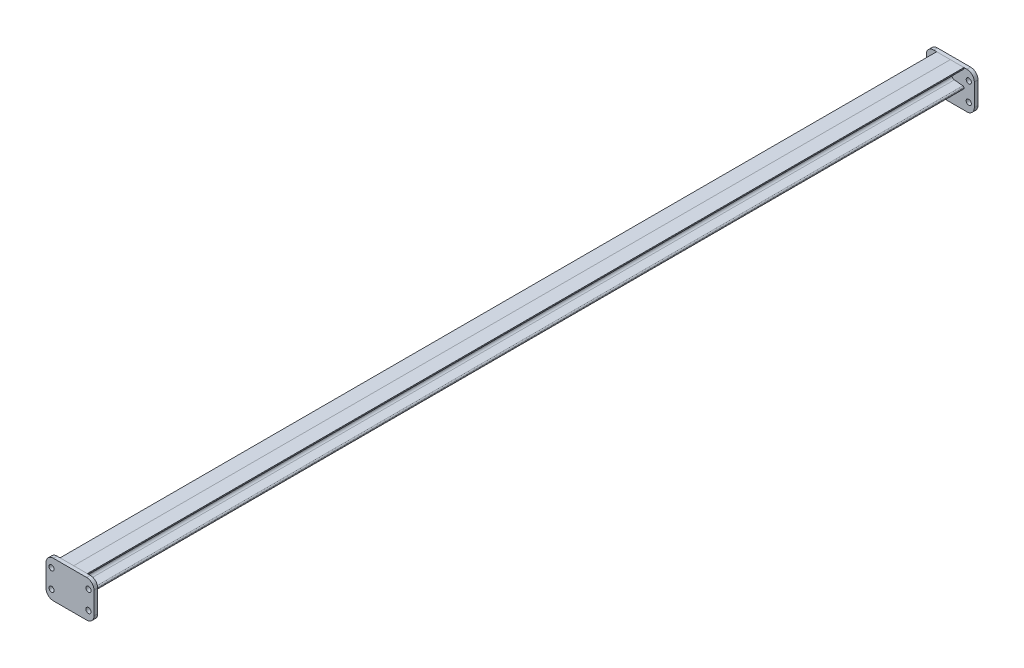
SolidWorks part; units mm, degrees
material "普通碳钢"
ref_plane "前视基准面" through (0, 0, 0) normal (0, 0, 1) x (1, 0, 0)
ref_plane "上视基准面" through (0, 0, 0) normal (0, 1, 0) x (1, 0, 0)
ref_plane "右视基准面" through (0, 0, 0) normal (1, 0, 0) x (0, 0, -1)
sketch "草图1" plane through (0, 0, 0) normal (1, 0, 0) x (0, 0, -1)
  line L0 (0, 0) -> (2374, 0)
  dimension "D1" = 2374
other "槽钢 5#(1)"
ref_plane "基准面1" through (0, 0, 0) normal (0, 0, -1) x (1, 0, 0)
sketch "草图12" plane through (0, 0, 0) normal (0, 0, -1) x (1, 0, 0)
  line L0 (0, -25) -> (37, -25)
  line L1 (37, -25) -> (37, -22.7923)
  line L2 (33.8482, -19.3097) -> (10.8035, -17.0055)
  line L3 (4.5, -10.0402) -> (4.5, 10.0402)
  line L4 (10.8035, 17.0055) -> (33.8482, 19.3097)
  line L5 (37, 22.7923) -> (37, 25)
  line L6 (37, 25) -> (0, 25)
  line L7 (0, 25) -> (0, -25)
  line L8 (20.75, 18) -> (20.75, -18) construction
  line L9 (0, 0) -> (4.5, 0) construction
  line L10 (4.5, 10.0402) -> (4.5, 35) construction
  line L11 (4.5, 35) -> (20.75, 35) construction
  line L12 (20.75, 35) -> (37, 35) construction
  line L13 (37, 35) -> (37, 25) construction
  line L14 (20.75, 35) -> (20.75, 18) construction
  arc A0 (10.8035, -17.0055) -> (4.5, -10.0402) centre (11.5, -10.0402) cw
  arc A1 (4.5, 10.0402) -> (10.8035, 17.0055) centre (11.5, 10.0402) cw
  arc A2 (37, -22.7923) -> (33.8482, -19.3097) centre (33.5, -22.7923) ccw
  arc A3 (33.8482, 19.3097) -> (37, 22.7923) centre (33.5, 22.7923) ccw
  point P2 (0, 0)
  point P19 (0, -25)
  point P20 (0, 25)
  point P22 (0, -25)
  point P23 (37, -25)
  point P24 (37, 25)
  point P26 (37, -19.6248)
  point P27 (11.5, 10.0402)
  point P28 (11.5, -10.0402)
  point P29 (37, 19.6248)
  dimension "D7" = 7
  dimension "D9" = 3.5
  dimension "D1" = 5.71
  dimension "D2" = 10
  dimension "D3" = 50
  dimension "D4" = 37
  dimension "D5" = 4.5
  dimension "D6" = 7
  dimension "D8" = 5.71
other "槽钢 5#(2)"
ref_plane "基准面2" through (0, 0, 0) normal (0, 0, -1) x (-1, 0, 0)
sketch "草图13" plane through (0, 0, 0) normal (0, 0, -1) x (-1, 0, 0)
  line L0 (0, -25) -> (37, -25)
  line L1 (37, -25) -> (37, -22.7923)
  line L2 (33.8482, -19.3097) -> (10.8035, -17.0055)
  line L3 (4.5, -10.0402) -> (4.5, 10.0402)
  line L4 (10.8035, 17.0055) -> (33.8482, 19.3097)
  line L5 (37, 22.7923) -> (37, 25)
  line L6 (37, 25) -> (0, 25)
  line L7 (0, 25) -> (0, -25)
  line L8 (20.75, 18) -> (20.75, -18) construction
  line L9 (0, 0) -> (4.5, 0) construction
  line L10 (4.5, 10.0402) -> (4.5, 35) construction
  line L11 (4.5, 35) -> (20.75, 35) construction
  line L12 (20.75, 35) -> (37, 35) construction
  line L13 (37, 35) -> (37, 25) construction
  line L14 (20.75, 35) -> (20.75, 18) construction
  arc A0 (10.8035, -17.0055) -> (4.5, -10.0402) centre (11.5, -10.0402) cw
  arc A1 (4.5, 10.0402) -> (10.8035, 17.0055) centre (11.5, 10.0402) cw
  arc A2 (37, -22.7923) -> (33.8482, -19.3097) centre (33.5, -22.7923) ccw
  arc A3 (33.8482, 19.3097) -> (37, 22.7923) centre (33.5, 22.7923) ccw
  point P2 (0, 0)
  point P19 (0, -25)
  point P20 (0, 25)
  point P22 (0, -25)
  point P23 (37, -25)
  point P24 (37, 25)
  point P26 (37, -19.6248)
  point P27 (11.5, 10.0402)
  point P28 (11.5, -10.0402)
  point P29 (37, 19.6248)
  dimension "D7" = 7
  dimension "D9" = 3.5
  dimension "D1" = 5.71
  dimension "D2" = 10
  dimension "D3" = 50
  dimension "D4" = 37
  dimension "D5" = 4.5
  dimension "D6" = 7
  dimension "D8" = 5.71
sketch "草图14" plane through (0, 0, 0) normal (0, 0, 1) x (1, 0, 0)
  line L0 (0, 25) -> (37, 25) construction
  line L1 (75, 0) -> (-65, 0) construction
  line L2 (45, 25) -> (-45, 25)
  line L3 (65, 5) -> (65, -55)
  line L4 (45, -75) -> (-45, -75)
  line L5 (-65, 5) -> (-65, -55)
  line L6 (75, -50) -> (-65, -50) construction
  line L7 (75, 25) -> (-65, 25) construction
  arc A0 (-45, -75) -> (-65, -55) centre (-45, -55) cw
  arc A1 (65, -55) -> (45, -75) centre (45, -55) cw
  arc A2 (45, 25) -> (65, 5) centre (45, 5) cw
  arc A3 (-45, 25) -> (-65, 5) centre (-45, 5) ccw
  point P13 (-65, -75)
  point P19 (65, 25)
  dimension "D5" = 20
  dimension "D1" = 130
  dimension "D2" = 100
  dimension "D3" = 25
  dimension "D4" = 50
extrude "凸台-拉伸1" add sketch "草图14" along normal blind 10 separate body
sketch "草图15" plane through (0, 0, 10) normal (0, 0, 1) x (1, 0, 0)
  line L0 (0, 25) -> (0, -75) construction
  line L1 (45, 25) -> (-45, 25) construction
  line L2 (-45, -75) -> (45, -75) construction
  line L5 (-50, 25) -> (-50, -75) construction
  line L7 (50, 25) -> (50, -75) construction
  line L8 (-65, 0) -> (65, 0) construction
  line L9 (-65, 5) -> (-65, -55) construction
  line L10 (65, -55) -> (65, 5) construction
  line L11 (-65, -50) -> (65, -50) construction
  circle A0 centre (-50, 0) radius 7
  circle A1 centre (-50, -50) radius 7
  circle A2 centre (50, 0) radius 7
  circle A3 centre (50, -50) radius 7
  dimension "D5" = 14
  dimension "D1" = 50
  dimension "D2" = 50
  dimension "D3" = 50
  dimension "D4" = 25
extrude "切除-拉伸1" cut sketch "草图15" against normal up to next (10 mm away)
sketch "草图16" plane through (0, 0, -2374) normal (0, 0, -1) x (-1, 0, 0)
  line L4 (-65, 5) -> (-65, -55)
  line L5 (-45, -75) -> (45, -75)
  line L6 (65, -55) -> (65, 5)
  line L7 (45, 25) -> (-45, 25)
  line L8 (-65, 5) -> (-65, -55)
  line L9 (-45, -75) -> (45, -75)
  line L10 (65, -55) -> (65, 5)
  line L11 (45, 25) -> (-45, 25)
  arc A4 (45, -75) -> (65, -55) centre (45, -55) ccw
  arc A5 (45, -75) -> (65, -55) centre (45, -55) ccw
  arc A6 (65, 5) -> (45, 25) centre (45, 5) ccw
  arc A7 (65, 5) -> (45, 25) centre (45, 5) ccw
  arc A8 (-45, 25) -> (-65, 5) centre (-45, 5) ccw
  arc A9 (-45, 25) -> (-65, 5) centre (-45, 5) ccw
  arc A10 (-65, -55) -> (-45, -75) centre (-45, -55) ccw
  arc A11 (-65, -55) -> (-45, -75) centre (-45, -55) ccw
  dimension "D1" = 0
extrude "凸台-拉伸2" add sketch "草图16" along normal blind 10 separate body
sketch "草图17" plane through (0, 0, -2384) normal (0, 0, -1) x (-1, 0, 0)
  circle A0 centre (50, 0) radius 7 construction
  circle A1 centre (50, 0) radius 7
  circle A2 centre (50, -50) radius 7 construction
  circle A3 centre (50, -50) radius 7
  circle A4 centre (-50, -50) radius 7 construction
  circle A5 centre (-50, -50) radius 7
  circle A6 centre (-50, 0) radius 7 construction
  circle A7 centre (-50, 0) radius 7
extrude "切除-拉伸2" cut sketch "草图17" against normal up to next (10 mm away)
